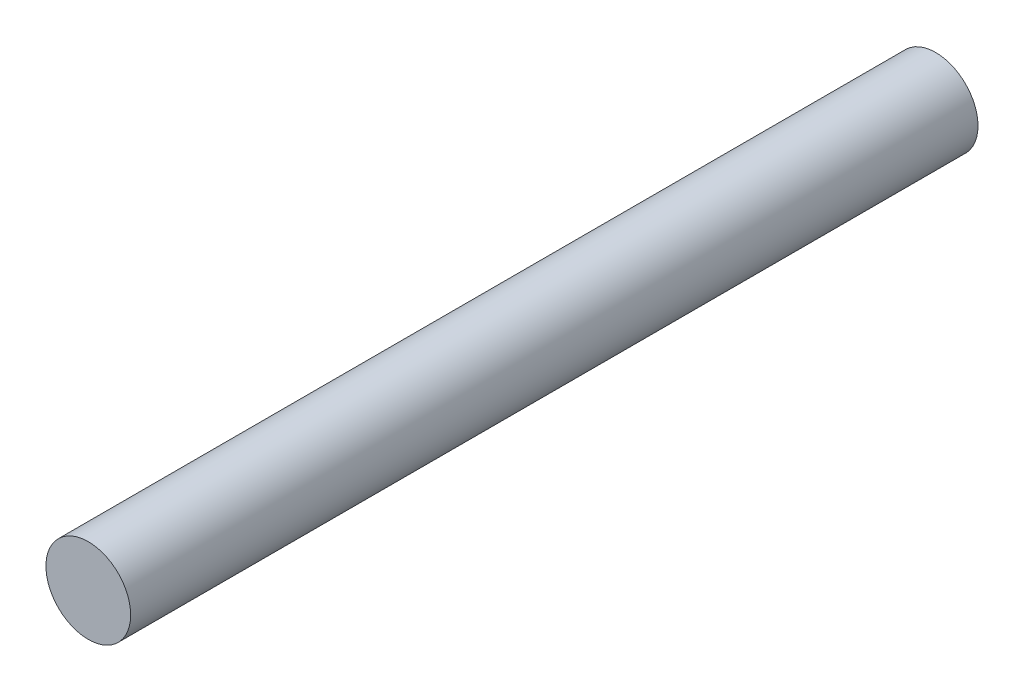
SolidWorks part; units mm, degrees
ref_plane "前视基准面" through (0, 0, 0) normal (0, 0, 1) x (1, 0, 0)
ref_plane "上视基准面" through (0, 0, 0) normal (0, 1, 0) x (1, 0, 0)
ref_plane "右视基准面" through (0, 0, 0) normal (1, 0, 0) x (0, 0, -1)
sketch "草图1" plane through (0, 0, 0) normal (0, 0, 1) x (1, 0, 0)
  circle A0 centre (0, 0) radius 4
  dimension "D1" = 8
extrude "凸台-拉伸1" add sketch "草图1" along normal blind 80
